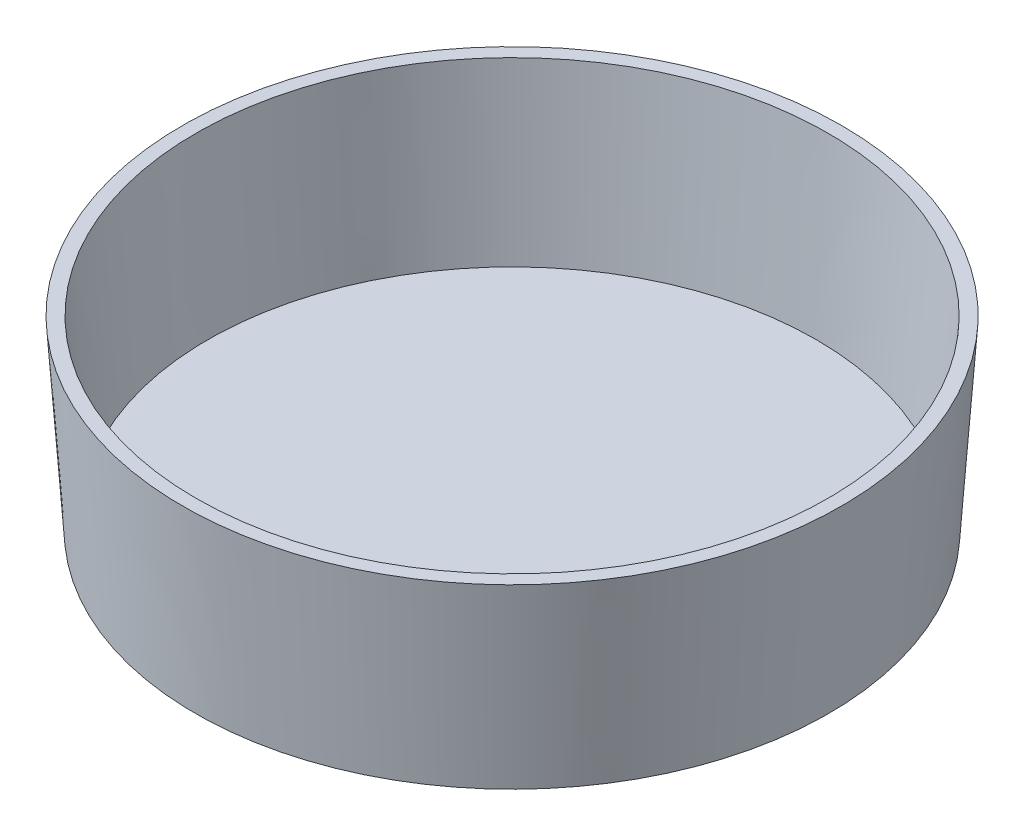
SolidWorks part; units mm, degrees
ref_plane "Front Plane" through (0, 0, 0) normal (0, 0, 1) x (1, 0, 0)
ref_plane "Top Plane" through (0, 0, 0) normal (0, 1, 0) x (1, 0, 0)
ref_plane "Right Plane" through (0, 0, 0) normal (1, 0, 0) x (0, 0, -1)
sketch "Sketch2" plane through (0, 0, 0) normal (0, 0, 1) x (1, 0, 0)
  line L0 (0, 0) -> (24.0221, 0)
  line L1 (0, 14.1224) -> (25, 14.1224)
  line L2 (25, 14.1224) -> (24.0221, 0)
  line L3 (0, 0) -> (0, 14.1224) construction
  line L4 (0, 0) -> (0, 14.1224)
  dimension "D1" = 24.0221
  dimension "D2" = 14.1224
  dimension "D3" = 25
revolve "Revolve1" add sketch "Sketch2" angle 360 about L3
shell "Shell1" thickness 1.016
sketch "Sketch3" plane through (0, 0, 0) normal (0, -1, 0) x (1, 0, 0)
  circle A1 centre (0, 0) radius 20.2883
  circle A2 centre (0, 0) radius 20.9741
  circle A3 centre (0, 0) radius 20.9741
  dimension "D1" = 3.048
  dimension "D2" = 0.6858
extrude "Boss-Extrude1" add sketch "Sketch3" along normal blind 0.762
